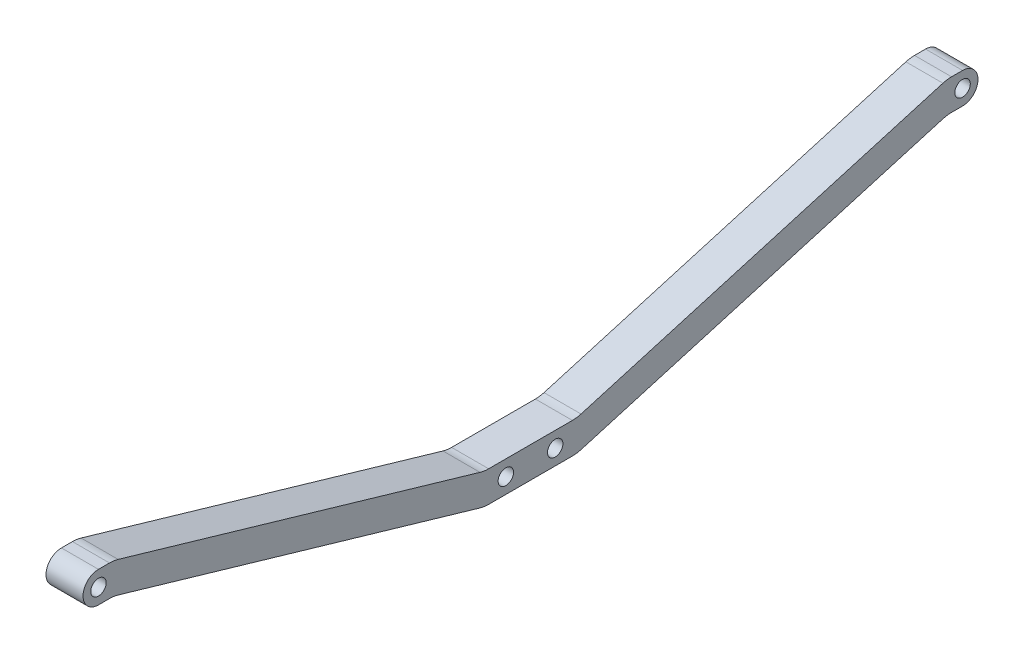
SolidWorks part; units mm, degrees
ref_plane "Alzado" through (0, 0, 0) normal (0, 0, 1) x (1, 0, 0)
ref_plane "Planta" through (0, 0, 0) normal (0, 1, 0) x (1, 0, 0)
ref_plane "Vista lateral" through (0, 0, 0) normal (1, 0, 0) x (0, 0, -1)
sketch "Croquis1" plane through (0, 0, 0) normal (1, 0, 0) x (0, 0, -1)
  line L0 (-140, 0) -> (140, 0) construction
  line L1 (0, 0) -> (0, -35) construction
  line L2 (-8, -35) -> (8, -35) construction
  line L3 (-15, -30) -> (15, -30)
  line L4 (-15, -40) -> (15, -40)
  line L5 (-15, -30) -> (-15, -40) construction
  line L6 (140, 5) -> (135, 5)
  line L7 (140, -5) -> (135, -5)
  line L8 (15, -40) -> (135, -5)
  line L9 (15, -30) -> (135, 5)
  line L10 (-140, 5) -> (-135, 5)
  line L11 (-140, -5) -> (-135, -5)
  line L12 (-15, -30) -> (-135, 5)
  line L13 (-15, -40) -> (-135, -5)
  circle A0 centre (-8, -35) radius 2.5
  circle A1 centre (8, -35) radius 2.5
  circle A2 centre (-140, 0) radius 2.5
  circle A3 centre (140, 0) radius 2.5
  arc A4 (-140, 5) -> (-140, -5) centre (-140, 0) ccw
  arc A5 (140, -5) -> (140, 5) centre (140, 0) ccw
  point P4 (0, 0)
  point P10 (0, -35)
  point P19 (0, -30)
  point P22 (0, -40)
  dimension "D4" = 5
  dimension "D5" = 5
  dimension "D6" = 5
  dimension "D7" = 5
  dimension "D8" = 10
  dimension "D9" = 10
  dimension "D1" = 280
  dimension "D2" = 35
  dimension "D3" = 16
  dimension "D10" = 30
  dimension "D11" = 30
  dimension "D12" = 5
  dimension "D13" = 10
  dimension "D14" = 5
  dimension "D15" = 5
  dimension "D16" = 5
  dimension "D17" = 5
extrude "Saliente-Extruir1" add sketch "Croquis1" along normal blind 12
fillet "Redondeo1" radius 10 8 edges at (6, -30, -15) (6, -30, 15) (6, -40, -15) (6, -40, 15) (6, -5, -135) (6, 5, -135) (6, -5, 135) (6, 5, 135)
